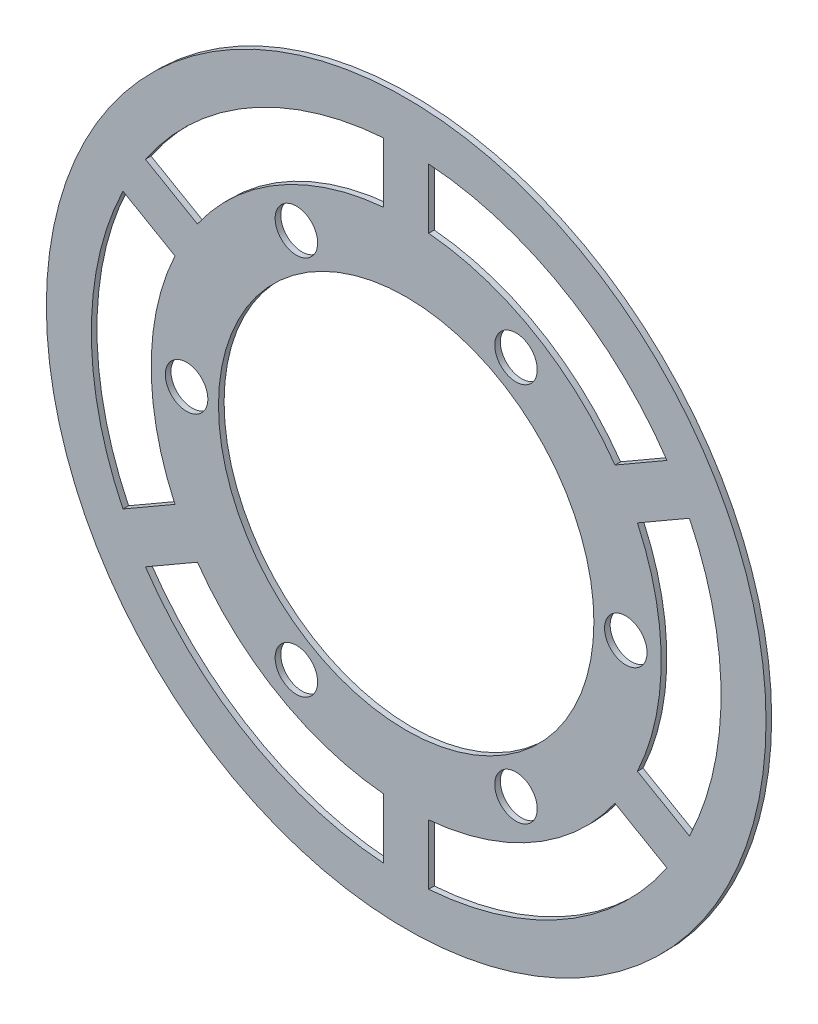
SolidWorks part; units mm, degrees
material "BUTYL"
ref_plane "Front Plane" through (0, 0, 0) normal (0, 0, 1) x (1, 0, 0)
ref_plane "Top Plane" through (0, 0, 0) normal (0, 1, 0) x (1, 0, 0)
ref_plane "Right Plane" through (0, 0, 0) normal (1, 0, 0) x (0, 0, -1)
sketch "Sketch1" plane through (0, 0, 0) normal (0, 0, 1) x (1, 0, 0)
  line L0 (-1.5846, 13.1549) -> (1.5846, 13.1549)
  line L1 (-1.5846, 17.9301) -> (-1.5846, 22.1684)
  line L2 (1.5846, 17.9301) -> (1.5846, 22.1684)
  line L4 (10.6002, 7.9498) -> (12.1848, 5.2051)
  line L5 (14.7356, 10.3374) -> (18.4061, 12.4566)
  line L6 (16.3203, 7.5927) -> (19.9908, 9.7119)
  line L8 (-12.1848, 5.2051) -> (-10.6002, 7.9498)
  line L9 (-16.3203, 7.5927) -> (-19.9908, 9.7119)
  line L10 (-14.7356, 10.3374) -> (-18.4061, 12.4566)
  line L12 (-12.1848, -5.2051) -> (-10.6002, -7.9498)
  line L13 (-16.3203, -7.5927) -> (-19.9908, -9.7119)
  line L14 (-14.7356, -10.3374) -> (-18.4061, -12.4566)
  line L16 (-1.5846, -13.1549) -> (1.5846, -13.1549)
  line L17 (-1.5846, -17.9301) -> (-1.5846, -22.1684)
  line L18 (1.5846, -17.9301) -> (1.5846, -22.1684)
  line L20 (10.6002, -7.9498) -> (12.1848, -5.2051)
  line L21 (14.7356, -10.3374) -> (18.4061, -12.4566)
  line L22 (16.3203, -7.5927) -> (19.9908, -9.7119)
  arc A0 (-1.586, 17.93) -> (-14.7349, 10.3385) centre (0, 0) ccw construction
  circle A1 centre (-15.5, 0) radius 1.5
  circle A2 centre (-7.75, 13.4234) radius 1.5
  circle A3 centre (7.75, 13.4234) radius 1.5
  circle A4 centre (15.5, 0) radius 1.5
  circle A5 centre (7.75, -13.4234) radius 1.5
  circle A6 centre (-7.75, -13.4234) radius 1.5
  arc A7 (-1.586, 17.93) -> (-14.7349, 10.3385) centre (0, 0) ccw
  arc A8 (-1.5846, 13.1549) -> (-10.6002, 7.9498) centre (0, 0) ccw
  arc A9 (-6.4162, 14.1097) -> (-9.0112, 12.6114) centre (0, 0) ccw construction
  arc A23 (14.7349, 10.3385) -> (1.586, 17.93) centre (0, 0) ccw construction
  arc A24 (14.7349, 10.3385) -> (1.586, 17.93) centre (0, 0) ccw
  arc A25 (-9.0112, -12.6114) -> (-6.4162, -14.1097) centre (0, 0) ccw construction
  arc A26 (16.3208, -7.5915) -> (16.3208, 7.5915) centre (0, 0) ccw construction
  arc A27 (16.3208, -7.5915) -> (16.3208, 7.5915) centre (0, 0) ccw
  arc A28 (12.1848, -5.2051) -> (12.1848, 5.2051) centre (0, 0) ccw
  arc A29 (-15.4274, 1.4982) -> (-15.4274, -1.4982) centre (0, 0) ccw construction
  arc A30 (1.586, -17.93) -> (14.7349, -10.3385) centre (0, 0) ccw construction
  arc A31 (1.586, -17.93) -> (14.7349, -10.3385) centre (0, 0) ccw
  arc A32 (1.5846, -13.1549) -> (10.6002, -7.9498) centre (0, 0) ccw
  arc A33 (-14.7349, -10.3385) -> (-1.586, -17.93) centre (0, 0) ccw construction
  arc A34 (-14.7349, -10.3385) -> (-1.586, -17.93) centre (0, 0) ccw
  arc A35 (-10.6002, -7.9498) -> (-1.5846, -13.1549) centre (0, 0) ccw
  arc A36 (-16.3208, 7.5915) -> (-16.3208, -7.5915) centre (0, 0) ccw construction
  arc A37 (-16.3208, 7.5915) -> (-16.3208, -7.5915) centre (0, 0) ccw
  arc A38 (-12.1848, 5.2051) -> (-12.1848, -5.2051) centre (0, 0) ccw
  arc A39 (10.6002, 7.9498) -> (1.5846, 13.1549) centre (0, 0) ccw
  circle A40 centre (0, 0) radius 13.25
  arc A41 (-16.3203, 7.5927) -> (-16.3203, -7.5927) centre (0, 0) ccw
  arc A42 (-19.9908, 9.7119) -> (-19.9908, -9.7119) centre (0, 0) ccw
  circle A43 centre (0, 0) radius 25.4
  arc A44 (-14.7356, -10.3374) -> (-1.5846, -17.9301) centre (0, 0) ccw
  arc A45 (-18.4061, -12.4566) -> (-1.5846, -22.1684) centre (0, 0) ccw
  arc A46 (1.5846, -17.9301) -> (14.7356, -10.3374) centre (0, 0) ccw
  arc A47 (1.5846, -22.1684) -> (18.4061, -12.4566) centre (0, 0) ccw
  arc A48 (16.3203, -7.5927) -> (16.3203, 7.5927) centre (0, 0) ccw
  arc A49 (19.9908, -9.7119) -> (19.9908, 9.7119) centre (0, 0) ccw
  arc A50 (14.7356, 10.3374) -> (1.5846, 17.9301) centre (0, 0) ccw
  arc A51 (18.4061, 12.4566) -> (1.5846, 22.1684) centre (0, 0) ccw
  arc A52 (-1.5846, 17.9301) -> (-14.7356, 10.3374) centre (0, 0) ccw
  arc A53 (-1.5846, 22.1684) -> (-18.4061, 12.4566) centre (0, 0) ccw
  point P43 (0, 0)
  point P44 (0, 0)
  point P45 (0, 0)
  point P47 (0, 0)
  point P48 (0, 0)
  point P53 (0, 0)
  dimension "D1" = 3
  dimension "D2" = 36
  dimension "D4" = 26.5
  dimension "D5" = 31
  dimension "D6" = 44.45
  dimension "D7" = 50.8
  dimension "D3" = 6
extrude "Boss-Extrude1" add sketch "Sketch1" along normal blind 0.3969 contours A0 A6 A5 A4 A3 A2 A1
